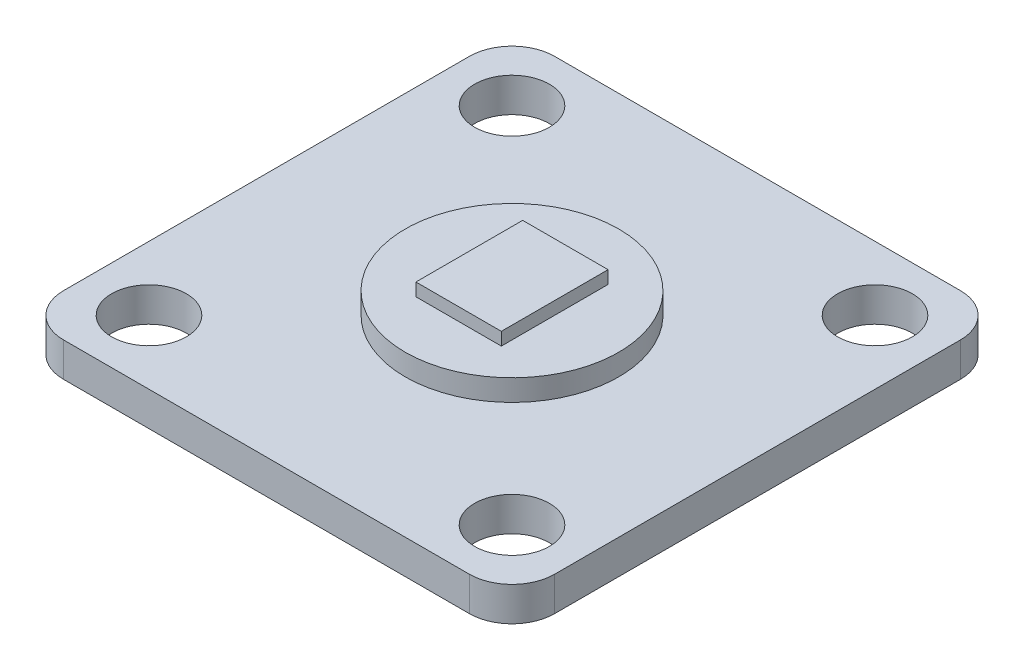
SolidWorks part; units mm, degrees
ref_plane "Front Plane" through (0, 0, 0) normal (0, 0, 1) x (1, 0, 0)
ref_plane "Top Plane" through (0, 0, 0) normal (0, 1, 0) x (1, 0, 0)
ref_plane "Right Plane" through (0, 0, 0) normal (1, 0, 0) x (0, 0, -1)
sketch "Sketch1" plane through (0, 0, 0) normal (0, 1, 0) x (1, 0, 0)
  line L1 (-9.5, -11.5) -> (9.5, -11.5)
  line L2 (-11.5, -9.5) -> (-11.5, 9.5)
  line L3 (-9.5, 11.5) -> (9.5, 11.5)
  line L4 (11.5, -9.5) -> (11.5, 9.5)
  line L5 (-11.5, -11.5) -> (11.5, 11.5) construction
  line L6 (-11.5, 11.5) -> (11.5, -11.5) construction
  circle A0 centre (8.5, 8.5) radius 1.75
  circle A1 centre (8.5, -8.5) radius 1.75
  circle A2 centre (-8.5, -8.5) radius 1.75
  circle A3 centre (-8.5, 8.5) radius 1.75
  arc A4 (-9.5, -11.5) -> (-11.5, -9.5) centre (-9.5, -9.5) cw
  arc A5 (9.5, -11.5) -> (11.5, -9.5) centre (9.5, -9.5) ccw
  arc A6 (9.5, 11.5) -> (11.5, 9.5) centre (9.5, 9.5) cw
  arc A7 (-11.5, 9.5) -> (-9.5, 11.5) centre (-9.5, 9.5) cw
  point P0 (0, 0)
  dimension "D3" = 17
  dimension "D4" = 17
  dimension "D5" = 17
  dimension "D6" = 0
  dimension "D7" = 3.5
  dimension "D8" = 3.5
  dimension "D9" = 3.5
  dimension "D10" = 3.5
  dimension "D11" = 2
  dimension "D1" = 23
  dimension "D2" = 23
extrude "Boss-Extrude1" add sketch "Sketch1" along normal blind 1.6
sketch "Sketch2" plane through (0, 1.6, 0) normal (0, 1, 0) x (1, 0, 0)
  line L1 (-2, -2.5) -> (2, -2.5)
  line L2 (-2, -2.5) -> (-2, 2.5)
  line L3 (-2, 2.5) -> (2, 2.5)
  line L4 (2, -2.5) -> (2, 2.5)
  line L5 (-2, -2.5) -> (2, 2.5) construction
  line L6 (-2, 2.5) -> (2, -2.5) construction
  point P0 (0, 0)
  dimension "D1" = 5
  dimension "D2" = 4
extrude "Boss-Extrude2" add sketch "Sketch2" along normal blind 1.6
sketch "Sketch3" plane through (0, 1.6, 0) normal (0, 1, 0) x (1, 0, 0)
  circle A0 centre (0, 0) radius 5
  dimension "D1" = 10
extrude "Boss-Extrude3" add sketch "Sketch3" along normal blind 1
